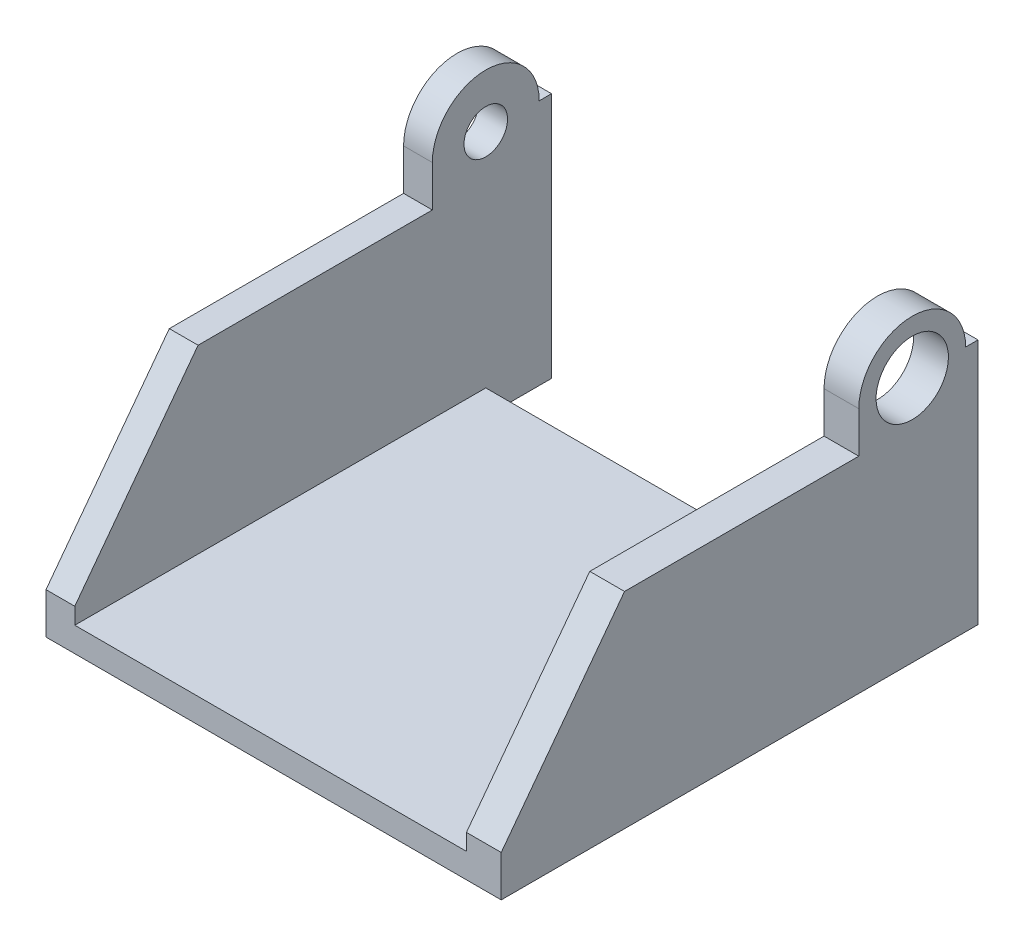
SolidWorks part; units mm, degrees
ref_plane "Front Plane" through (0, 0, 0) normal (0, 0, 1) x (1, 0, 0)
ref_plane "Top Plane" through (0, 0, 0) normal (0, 1, 0) x (1, 0, 0)
ref_plane "Right Plane" through (0, 0, 0) normal (1, 0, 0) x (0, 0, -1)
sketch "Sketch1" plane through (0, 0, 0) normal (0, 0, 1) x (1, 0, 0)
  line L0 (0, 0) -> (-23.825, 0) construction
  line L2 (-23.825, 0) -> (-27.325, 0)
  line L3 (-23.825, 0) -> (-23.825, -30)
  line L4 (-23.825, -30) -> (-27.325, -30)
  line L5 (-27.325, 0) -> (-27.325, -30)
  line L6 (-23.825, -30) -> (0, -30)
  line L7 (-23.825, -30) -> (-23.825, -27)
  line L8 (-23.825, -27) -> (0, -27)
  line L9 (0, -30) -> (0, -27)
  dimension "D1" = 23.825
  dimension "D2" = 3.5
  dimension "D3" = 30
  dimension "D4" = 3
extrude "Boss-Extrude1" add sketch "Sketch1" along normal blind 50 contours L2 L5 L4 L3 | L6 L9 L8 L3
sketch "Sketch2" plane through (-23.825, 0, 0) normal (1, 0, 0) x (0, 0, -1)
  line L1 (0, 0) -> (8, 0)
  line L2 (0, 0) -> (0, -30)
  line L3 (0, -30) -> (8, -30)
  line L4 (8, 0) -> (8, -30)
  circle A0 centre (0, 0) radius 1.5
  circle A1 centre (0, 0) radius 6.5
  line M1 (0, -27) -> (0, 0)
  line M2 (0, 0) -> (-50, 0)
  dimension "D1" = 3
  dimension "D2" = 13
  dimension "D3" = 8
extrude "Boss-Extrude2" add sketch "Sketch2" against normal blind 3.5 contours A1 L2 L3 L4 L1 M1 | L2 A1 L1 A0 | L1 A1 A0 M2
sketch "Sketch3" plane through (-27.325, 0, 0) normal (-1, 0, 0) x (0, 0, 1)
  circle A0 centre (0, 0) radius 1.5
extrude "Cut-Extrude1" cut sketch "Sketch3" against normal through all both and the other way through all
mirror "Mirror1" about plane through (0, 0, 50) normal (-1, 0, 0) of "Cut-Extrude1", "Boss-Extrude2", "Boss-Extrude1"
sketch "Sketch4" plane through (-27.325, 0, 0) normal (-1, 0, 0) x (0, 0, 1)
  circle A0 centre (0, 0) radius 2.5
  dimension "D1" = 5
extrude "Cut-Extrude2" cut sketch "Sketch4" against normal blind 3.15 and the other way through all
sketch "Sketch5" plane through (27.325, 0, 0) normal (1, 0, 0) x (0, 0, -1)
  circle A0 centre (0, 0) radius 2.9
  dimension "D1" = 5.8
extrude "Cut-Extrude3" cut sketch "Sketch5" against normal blind 7.15
sketch "Sketch6" plane through (-27.325, 0, 0) normal (-1, 0, 0) x (0, 0, 1)
  line L1 (50, 0) -> (25, 0)
  line L2 (50, 0) -> (50, -25)
  line L5 (35, -5) -> (50, -25)
  line L7 (6.5, 0) -> (50, 0)
  line L8 (6.5, 0) -> (6.5, -5)
  line L9 (6.5, -5) -> (35, -5)
  line L10 (50, 0) -> (50, -10)
  line M4 (50, 0) -> (6.5, 0)
  line M9 (50, -30) -> (50, 0)
  dimension "D1" = 5
  dimension "D2" = 25
  dimension "D3" = 5
extrude "Cut-Extrude4" cut sketch "Sketch6" against normal blind 7.15 contours L5 M4 M9
ref_plane "Plane1" through (0, 0, 0) normal (1, 0, 0) x (0, 0, -1)
mirror "Mirror2" about plane through (0, 0, 0) normal (1, 0, 0) of "Cut-Extrude4"
sketch "Sketch7" plane through (-24.175, 0, 0) normal (-1, 0, 0) x (0, 0, 1)
  circle A0 centre (0, 0) radius 1.5
  circle A1 centre (0, 0) radius 2.5
extrude "Boss-Extrude3" add sketch "Sketch7" along normal blind 0.65
sketch "Sketch9" plane through (27.325, 0, 0) normal (1, 0, 0) x (0, 0, -1)
  line L0 (-50, -30) -> (8, -30) construction
  line L1 (0, 0) -> (0, -19) construction
  line L8 (8, 0) -> (-6.5, 0)
  line L9 (8, 0) -> (8, -30)
  line L10 (8, -30) -> (-6.5, -30)
  line L11 (-6.5, 0) -> (-6.5, -3.7914)
  line L16 (-6.5, -30) -> (-52.6172, -30)
  line L18 (-6.5, -3.7914) -> (-52.6172, -3.7914)
  line L19 (-52.6172, -30) -> (-52.6172, -3.7914)
  circle A1 centre (0, 0) radius 6.5
  dimension "D1" = 14.5
extrude "Cut-Extrude5" cut sketch "Sketch9" against normal blind 0.4
sketch "Sketch12" plane through (26.925, 0, 0) normal (1, 0, 0) x (0, 0, -1)
  line L22 (8, 0) -> (6.5, 0)
  line L23 (-6.5, 0) -> (-6.5, -5)
  line L24 (-6.5, -5) -> (-35, -5)
  line L25 (-35, -5) -> (-50, -25)
  line L26 (-50, -25) -> (-50, -30)
  line L27 (-50, -30) -> (8, -30)
  line L28 (8, -30) -> (8, 0)
  line L29 (8, 0) -> (6.5, 0)
  line L30 (-6.5, 0) -> (-6.5, -5)
  line L31 (-6.5, -5) -> (-35, -5)
  line L32 (-35, -5) -> (-50, -25)
  line L33 (-50, -25) -> (-50, -30)
  line L34 (-50, -30) -> (8, -30)
  line L35 (8, -30) -> (8, 0)
  circle A0 centre (0, 0) radius 4.4
  arc A3 (6.5, 0) -> (-6.5, 0) centre (0, 0) ccw
  arc A4 (6.5, 0) -> (-6.5, 0) centre (0, 0) ccw
  dimension "D2" = 8.8
  dimension "D1" = 0
extrude "Boss-Extrude4" add sketch "Sketch12" along normal blind 1.13
sketch "Sketch13" plane through (-27.325, 0, 0) normal (-1, 0, 0) x (0, 0, 1)
  circle A0 centre (0, 0) radius 1.5
  circle A1 centre (0, 0) radius 2.5
extrude "Boss-Extrude5" add sketch "Sketch13" along direction (1, 0, 0) on the side against the normal up to surface (2.5 mm away)
sketch "Sketch14" plane through (-27.325, 0, 0) normal (-1, 0, 0) x (0, 0, 1)
  circle A0 centre (0, 0) radius 2.65
  dimension "D1" = 5.3
extrude "Cut-Extrude7" cut sketch "Sketch14" against normal blind 5.05
sketch "Sketch10" plane through (26.925, 0, 0) normal (1, 0, 0) x (0, 0, -1)
  circle A0 centre (0, 0) radius 4.4
  dimension "D1" = 8.8
extrude "Cut-Extrude8" cut sketch "Sketch10" along normal blind 10 and the other way blind 10
